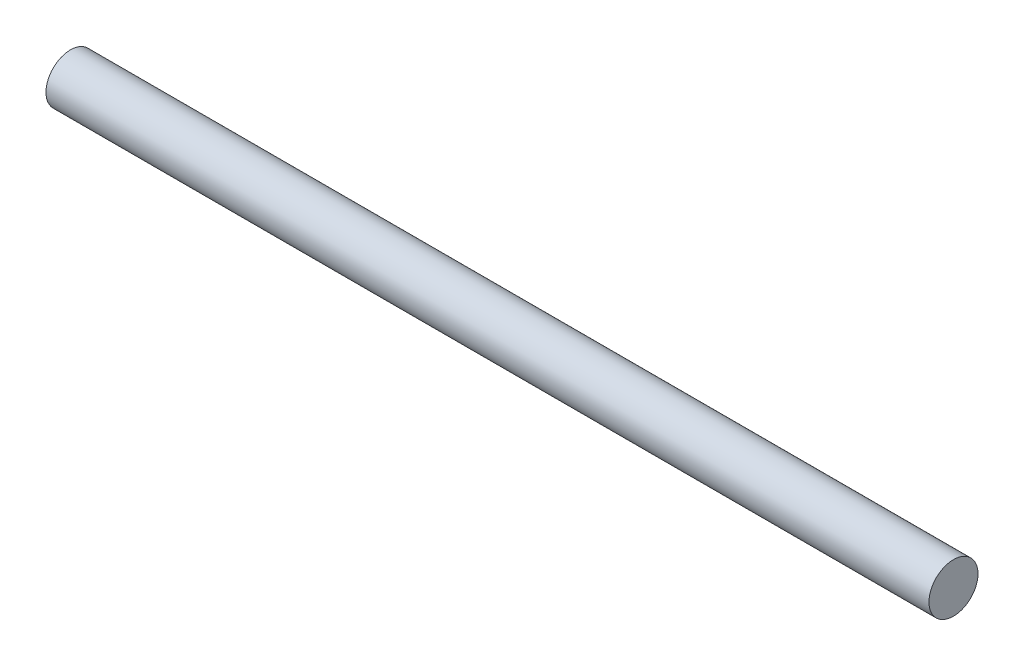
SolidWorks part; units mm, degrees
material "Cast Stainless Steel"
ref_plane "Front" through (0, 0, 0) normal (0, 0, 1) x (1, 0, 0)
ref_plane "Top" through (0, 0, 0) normal (0, 1, 0) x (1, 0, 0)
ref_plane "Right" through (0, 0, 0) normal (1, 0, 0) x (0, 0, -1)
sketch "Sketch2" plane through (0, 0, 0) normal (1, 0, 0) x (0, 0, -1)
  circle A0 centre (0, 0) radius 6.35
  dimension "D1" = 12.7
extrude "Boss-Extrude1" add sketch "Sketch2" along normal blind 228.6
